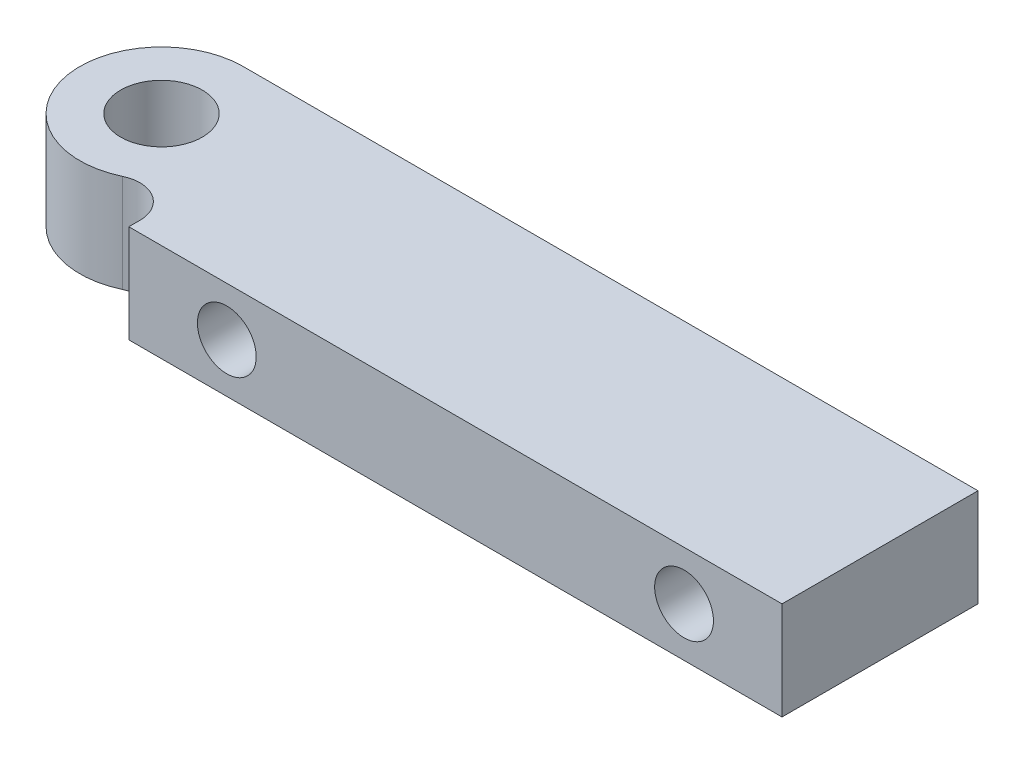
SolidWorks part; units mm, degrees
ref_plane "Front Plane" through (0, 0, 0) normal (0, 0, 1) x (1, 0, 0)
ref_plane "Top Plane" through (0, 0, 0) normal (0, 1, 0) x (1, 0, 0)
ref_plane "Right Plane" through (0, 0, 0) normal (1, 0, 0) x (0, 0, -1)
sketch "Sketch1" plane through (0, 0, 0) normal (0, 1, 0) x (1, 0, 0)
  line L0 (0, 6.35) -> (12.3665, 6.35)
  line L1 (12.3665, 6.35) -> (57.15, 6.35)
  line L2 (6.35, 0) -> (6.35, -8.89)
  line L3 (6.35, -8.89) -> (57.15, -8.89)
  line L4 (57.15, 6.35) -> (57.15, -8.89)
  circle A0 centre (0, 0) radius 3.175
  arc A1 (0, 6.35) -> (6.35, 0) centre (0, 0) ccw
  dimension "D1" = 12.7
  dimension "D2" = 6.35
  dimension "D3" = 6.35
  dimension "D4" = 50.8
  dimension "D5" = 15.24
extrude "Boss-Extrude1" add sketch "Sketch1" along normal mid plane 7.62
fillet "Fillet1" radius 2.54 1 edges at (6.35, 0, 0)
sketch "Sketch2" plane through (0, 0, 8.89) normal (0, 0, 1) x (1, 0, 0)
  circle A0 centre (49.53, 0) radius 1.8987 construction
  circle A1 centre (13.97, 0) radius 1.8987 construction
  circle A2 centre (49.53, 0) radius 1.8986
  circle A3 centre (13.97, 0) radius 1.8986
  circle A4 centre (13.97, 0) radius 2.286
  circle A5 centre (49.53, 0) radius 2.286
  dimension "D1" = 4.572
  dimension "D2" = 4.572
extrude "Cut-Extrude1" cut sketch "Sketch2" against normal blind 5.08 contours A4 | A5 | A3 | A2
